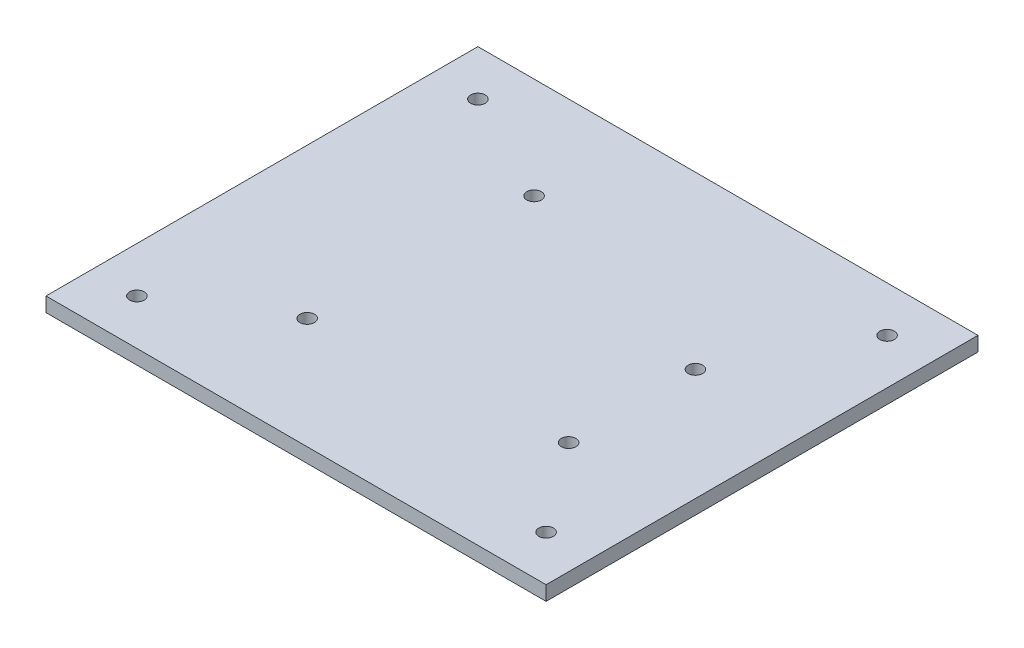
SolidWorks part; units mm, degrees
ref_plane "Front Plane" through (0, 0, 0) normal (0, 0, 1) x (1, 0, 0)
ref_plane "Top Plane" through (0, 0, 0) normal (0, 1, 0) x (1, 0, 0)
ref_plane "Right Plane" through (0, 0, 0) normal (1, 0, 0) x (0, 0, -1)
sketch "Sketch1" plane through (0, 0, 0) normal (0, 1, 0) x (1, 0, 0)
  line L0 (-55, 47.5) -> (55, -47.5)
  line L1 (-55, 47.5) -> (55, 47.5)
  line L2 (-55, 47.5) -> (-55, -47.5)
  line L3 (-55, -47.5) -> (55, -47.5)
  line L4 (55, 47.5) -> (55, -47.5)
  line L5 (55, 47.5) -> (-55, -47.5)
  point P4 (0, 0)
  dimension "D1" = 95
  dimension "D2" = 110
extrude "Boss-Extrude1" add sketch "Sketch1" along normal blind 3.18 contours L5 L0 L2 | L0 L5 L3 | L4 L5 L0 | L5 L1 L0
sketch "Sketch2" plane through (0, 3.18, 0) normal (0, 1, 0) x (1, 0, 0)
  line L0 (-22, -23.05) -> (-22, 25.25) construction
  line L1 (30.4, -17.95) -> (18.7033, -17.95)
  line L2 (-22, -23.05) -> (18.7033, -23.05)
  line L3 (18.7033, -23.05) -> (18.7033, -17.95)
  line L4 (-55, 47.5) -> (55, 47.5) construction
  line L6 (-55, 47.5) -> (-55, -47.5) construction
  circle A0 centre (-20.4, 25.25) radius 1.6
  circle A1 centre (-22, -23.05) radius 1.6
  circle A2 centre (30.4, 9.95) radius 1.6
  circle A3 centre (30.4, -17.95) radius 1.6
  dimension "D1" = 3.2
  dimension "D5" = 34.6
  dimension "D6" = 48.3
  dimension "D2" = 50.8
  dimension "D3" = 27.9
  dimension "D4" = 5.1
  dimension "D7" = 37.55
extrude "Cut-Extrude1" cut sketch "Sketch2" against normal blind 3.18
sketch "Sketch3" plane through (0, 3.18, 0) normal (0, 1, 0) x (1, 0, 0)
  line L0 (55, 47.5) -> (55, -47.5) construction
  line L1 (-55, 47.5) -> (55, 47.5) construction
  line L2 (-55, -47.5) -> (55, -47.5) construction
  line L3 (-55, 47.5) -> (-55, -47.5) construction
  circle A0 centre (45, 37.5) radius 1.6
  circle A1 centre (45, -37.5) radius 1.6
  circle A2 centre (-45, 37.5) radius 1.6
  circle A3 centre (-45, -37.5) radius 1.6
  dimension "D1" = 3.2
  dimension "D2" = 10
  dimension "D3" = 10
  dimension "D4" = 10
  dimension "D5" = 10
  dimension "D6" = 10
  dimension "D7" = 10
  dimension "D8" = 10
  dimension "D9" = 10
extrude "Cut-Extrude2" cut sketch "Sketch3" against normal blind 10
